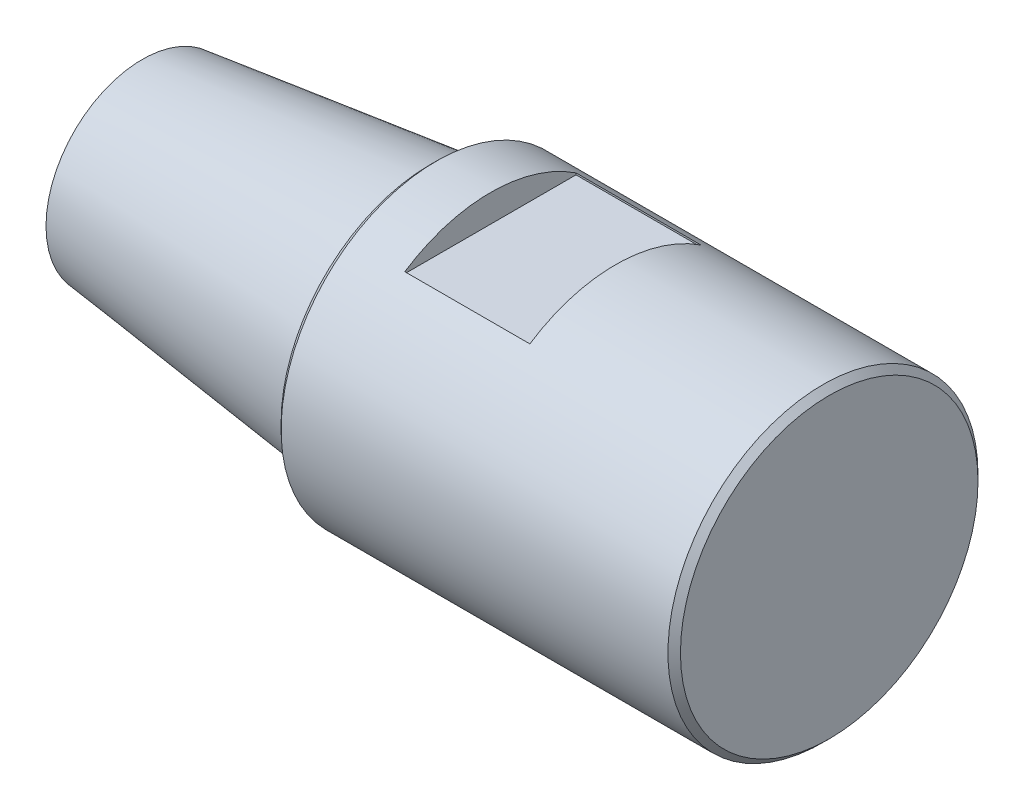
SolidWorks part; units mm, degrees
material "POM Acetalkopolymer"
ref_plane "Ebene vorne" through (0, 0, 0) normal (0, 0, 1) x (1, 0, 0)
ref_plane "Ebene oben" through (0, 0, 0) normal (0, 1, 0) x (1, 0, 0)
ref_plane "Ebene rechts" through (0, 0, 0) normal (1, 0, 0) x (0, 0, -1)
sketch "Skizze1" plane through (0, 0, 0) normal (0, 1, 0) x (1, 0, 0)
  line L0 (-46, 0) -> (0, 0) construction
  line L1 (-46, 0) -> (-46, 15.4)
  line L2 (0, 0) -> (0, 20.905)
  line L3 (-46, 15.4) -> (0, 20.905)
  line L4 (-46, 0) -> (0, 0)
  dimension "D1" = 46
  dimension "D2" = 15.4
  dimension "D3" = 20.905
  dimension "D4" = 0
revolve "Rotation1" add sketch "Skizze1" angle 360 about L0
sketch "Skizze2" plane through (0, 0, 0) normal (1, 0, 0) x (0, 0, -1)
  circle A0 centre (0, 0) radius 24.795
  dimension "D1" = 49.59
extrude "Aufsatz-Linear austragen1" add sketch "Skizze2" along normal blind 63.87
ref_plane "Ebene1" through (63.87, 0, 0) normal (1, 0, 0) x (0, 0, -1)
ref_plane "Ebene2" through (0, 24.795, 0) normal (0, 1, 0) x (1, 0, 0)
sketch "Skizze8" plane through (0, 24.795, 0) normal (0, 1, 0) x (1, 0, 0)
  line L0 (63.87, 0) -> (0, 0) construction
  line L1 (9.68, -13.69) -> (29.68, -13.69)
  line L2 (9.68, -13.69) -> (9.68, 13.69)
  line L3 (9.68, 13.69) -> (29.68, 13.69)
  line L4 (29.68, -13.69) -> (29.68, 13.69)
  line L5 (0, 24.795) -> (0, -24.795) construction
  point P0 (48.8685, 0)
  dimension "D1" = 20
  dimension "D2" = 27.38
  dimension "D3" = 13.69
  dimension "D4" = 9.68
  dimension "D5" = 48.8685
extrude "Schnitt-Linear austragen1" cut sketch "Skizze8" against normal blind 4.4
pattern_circular "Kreismuster1" count 2 over 360 about axis through (0, 0, 0) along (1, 0, 0) of "Schnitt-Linear austragen1"
chamfer "Fase1" distance 1 angle 45 2 edges at (63.87, 0, -24.795) (0, 0, -24.795)
